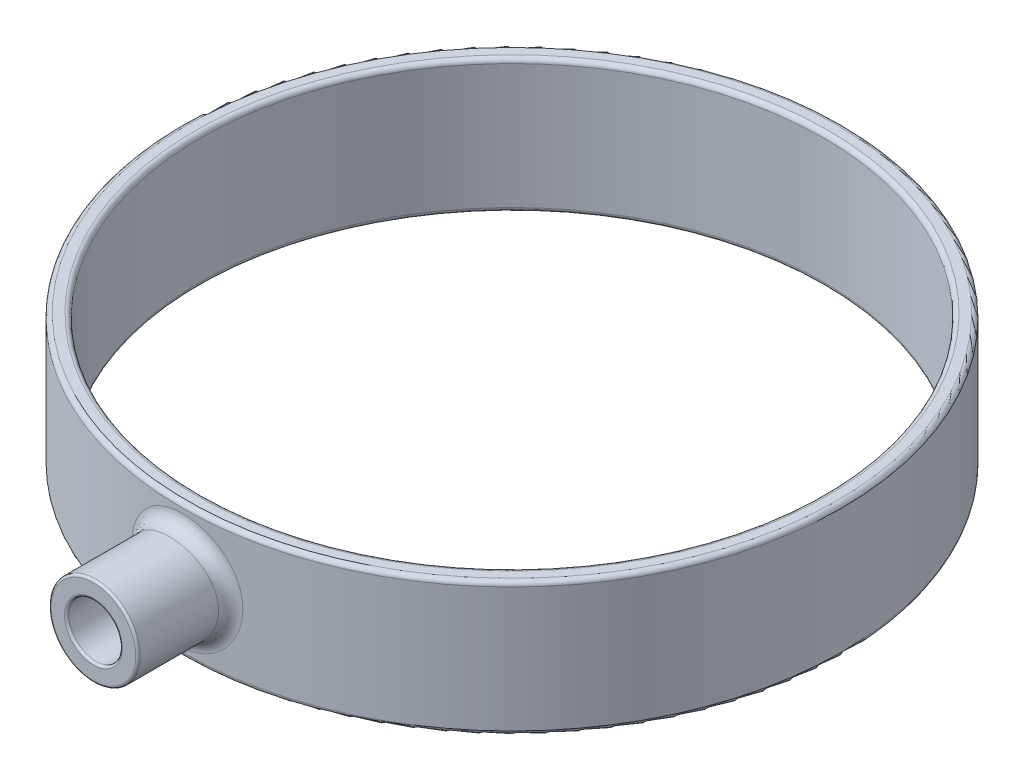
SolidWorks part; units mm, degrees
ref_plane "Front" through (0, 0, 0) normal (0, 0, 1) x (1, 0, 0)
ref_plane "Top" through (0, 0, 0) normal (0, 1, 0) x (1, 0, 0)
ref_plane "Right" through (0, 0, 0) normal (1, 0, 0) x (0, 0, -1)
sketch "Sketch1" plane through (0, 0, 0) normal (0, 0, 1) x (1, 0, 0)
  line L0 (0, 15.2591) -> (0, -21.4682) construction
  line L1 (35, 7.5) -> (37, 7.5)
  line L2 (35, 7.5) -> (35, -7.5)
  line L3 (35, -7.5) -> (37, -7.5)
  line L4 (37, 7.5) -> (37, -7.5)
  line L5 (-25.6474, 0) -> (45.9998, 0) construction
  dimension "D1" = 2
  dimension "D2" = 15
  dimension "D3" = 70
  dimension "D4" = 7.5
revolve "Revolve1" add sketch "Sketch1" angle 360 about L0
ref_plane "Plane1" through (0, 0, 37) normal (0, 0, 1) x (1, 0, 0)
ref_plane "Plane2" through (0, 0, 47) normal (0, 0, 1) x (1, 0, 0)
sketch "Sketch2" plane through (0, 0, 47) normal (0, 0, 1) x (1, 0, 0)
  circle A0 centre (0, 0) radius 5
  dimension "D1" = 10
extrude "Boss-Extrude1" add sketch "Sketch2" against normal up to body separate body
sketch "Sketch4" plane through (0, 0, 47) normal (0, 0, 1) x (1, 0, 0)
  circle A0 centre (0, 0) radius 3
extrude "Cut-Extrude1" cut sketch "Sketch4" against normal blind 10
fillet "Fillet2" radius 0.25 2 edges at (5, 0, 47) (3, 0, 47)
fillet "Fillet3" radius 1.5 1 edges at (-4.8777, -1.0989, 36.6771)
fillet "Fillet4" radius 0.5 4 edges at (0, -7.5, 35) (0, -7.5, 37) (0, 7.5, 37) (0, 7.5, 35)
